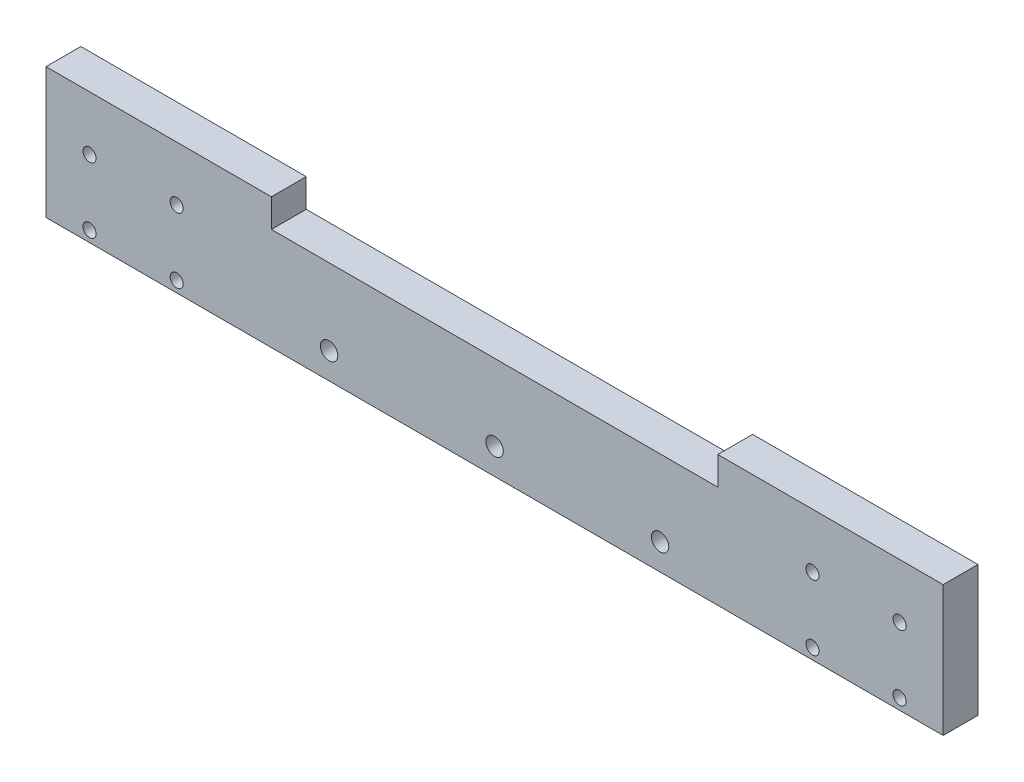
SolidWorks part; units mm, degrees
ref_plane "Front" through (0, 0, 0) normal (0, 0, 1) x (1, 0, 0)
ref_plane "Top" through (0, 0, 0) normal (0, 1, 0) x (1, 0, 0)
ref_plane "Right" through (0, 0, 0) normal (1, 0, 0) x (0, 0, -1)
sketch "Esquisse1" plane through (0, 0, 0) normal (0, 0, 1) x (1, 0, 0)
  line L1 (0, 0) -> (206, 0)
  line L2 (0, 0) -> (0, 30)
  line L3 (0, 30) -> (206, 30)
  line L4 (206, 0) -> (206, 30)
  line L5 (51.75, 30) -> (154.25, 30) construction
  line L6 (51.75, 30) -> (51.75, 23.5)
  line L7 (51.75, 23.5) -> (154.25, 23.5)
  line L8 (154.25, 30) -> (154.25, 23.5)
  point P9 (103, 30)
  point P10 (103, 30)
  point P11 (-16.136, 26.435)
  point P12 (33.599, 25.5053)
  dimension "D1" = 102.5
  dimension "D2" = 206
  dimension "D3" = 23.5
  dimension "D4" = 30
extrude "Boss.-Extru.1" add sketch "Esquisse1" along normal blind 8 contours L3 L8 L7 L6 L2 L1 L4
sketch "Esquisse2" plane through (0, 0, 8) normal (0, 0, 1) x (1, 0, 0)
  line L0 (141, 6) -> (65, 6) construction
  line L3 (103, 0) -> (103, 13.0932) construction
  line L4 (0, 0) -> (206, 0) construction
  circle A0 centre (103, 6) radius 2
  circle A1 centre (141, 6) radius 2
  circle A2 centre (65, 6) radius 2
  point P5 (103, 6)
  dimension "D2" = 4
  dimension "D1" = 76
  dimension "D3" = 6
extrude "Enlèv. mat.-Extru.1" cut sketch "Esquisse2" against normal through all
sketch "Esquisse3" plane through (0, 0, 8) normal (0, 0, 1) x (1, 0, 0)
  line L0 (196, 2.5) -> (196, 17.5) construction
  line L1 (196, 10) -> (176, 10) construction
  line L2 (176, 2.5) -> (176, 17.5) construction
  line L3 (0, 0) -> (206, 0) construction
  line L4 (206, 0) -> (206, 30) construction
  circle A0 centre (176, 17.5) radius 1.5
  circle A1 centre (196, 17.5) radius 1.5
  circle A2 centre (196, 2.5) radius 1.5
  circle A3 centre (176, 2.5) radius 1.5
  point P7 (176, 10)
  dimension "D1" = 3
  dimension "D2" = 15
  dimension "D3" = 10
  dimension "D4" = 10
  dimension "D5" = 20
extrude "Enlèv. mat.-Extru.2" cut sketch "Esquisse3" against normal blind 5
ref_plane "Plan1" through (103, 0, 0) normal (1, 0, 0) x (0, 0, -1)
mirror "Symétrie1" about plane through (103, 0, 0) normal (1, 0, 0) of "Enlèv. mat.-Extru.2"
